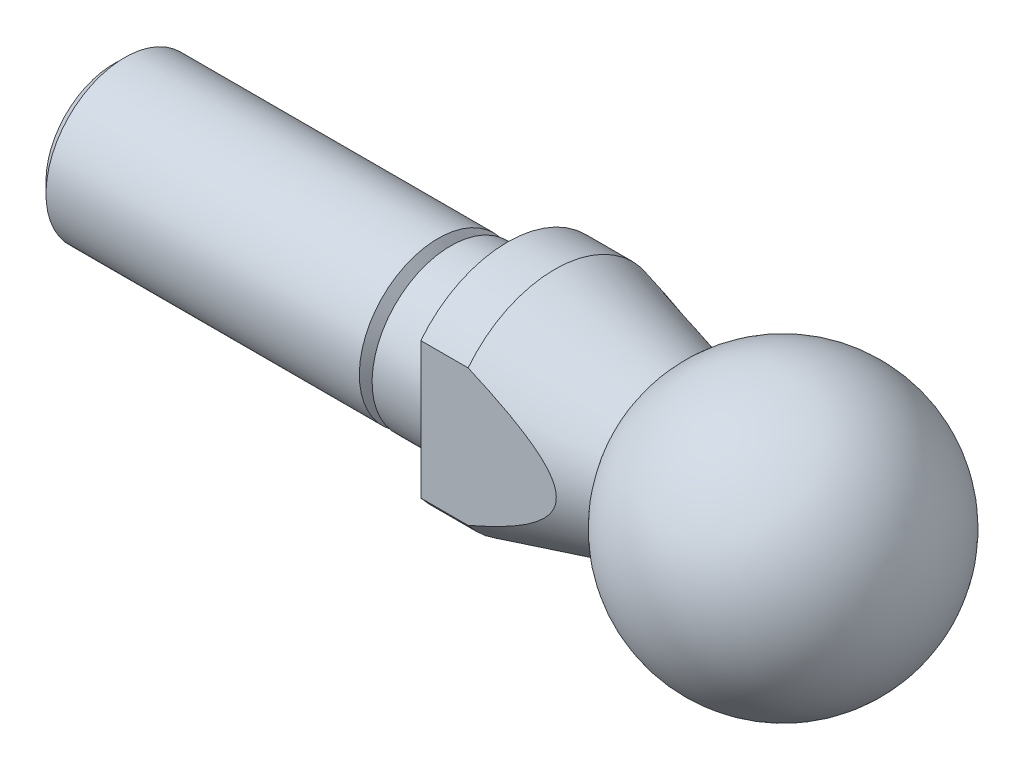
SolidWorks part; units mm, degrees
material "220M07"
ref_plane "Front Plane" through (0, 0, 0) normal (0, 0, 1) x (1, 0, 0)
ref_plane "Top Plane" through (0, 0, 0) normal (0, 1, 0) x (1, 0, 0)
ref_plane "Right Plane" through (0, 0, 0) normal (1, 0, 0) x (0, 0, -1)
sketch "Sketch1" plane through (0, 0, 0) normal (0, 0, 1) x (1, 0, 0)
  line L0 (-9.813, 0) -> (9.813, 0) construction
  line L3 (-14.5, 7) -> (-17.5, 7)
  line L4 (-17.5, 7) -> (-17.5, 5)
  line L5 (-17.5, 5) -> (-21.0959, 5)
  line L6 (-21.0959, 5) -> (-21.5, 4.3)
  line L7 (-21.5, 4.3) -> (-21.9041, 5)
  line L8 (-21.9041, 5) -> (-41.8, 5)
  line L10 (-42.5, 4.3) -> (-42.5, 0)
  line L11 (-42.5, 0) -> (8.75, 0)
  line L12 (-42.5, 4.3) -> (-41.8, 5)
  line L13 (-14.5, 7) -> (-7.1578, 5.0327)
  arc A0 (8.75, 0) -> (-7.1578, 5.0327) centre (0, 0) ccw
  point P4 (0, 0)
  dimension "D1" = 60
  dimension "Ball DIam" = 17.5
  dimension "Thd D" = 10
  dimension "Thd L" = 21
  dimension "D2" = 45
  dimension "Boss Diam" = 14
  dimension "Boss Thickness" = 3
  dimension "Centre L" = 42.5
  dimension "Thd Min" = 8.6
  dimension "D4" = 15
  dimension "Up To Shoulder" = 25
revolve "Body Revolve" add sketch "Sketch1" angle 360 about L0
ref_plane "Plane1" through (-7.1578, 0, 0) normal (1, 0, 0) x (0, 0, -1)
sketch "Sketch2" plane through (-17.5, 0, 0) normal (-1, 0, 0) x (0, 0, 1)
  line L1 (-5.5, -7) -> (5.5, -7)
  line L2 (-5.5, -7) -> (-5.5, 7)
  line L3 (-5.5, 7) -> (5.5, 7)
  line L4 (5.5, -7) -> (5.5, 7)
  line L5 (-5.5, -7) -> (5.5, 7) construction
  line L6 (-5.5, 7) -> (5.5, -7) construction
  circle A0 centre (0, 0) radius 7 construction
  point P0 (0, 0)
  dimension "S af" = 11
extrude "Cut-Extrude1" cut sketch "Sketch2" against normal up to surface (10.3422 mm away) flip side to cut up to plane "Plane1"
thread "Thread1" pitch 1 start angle 0, offset 2, length 0, pitch 1, diameter 6
ref_plane "Plane2" through (-28.95, 0, -3) normal (0, -1, 0) x (0, 0, -1)
sketch "Thread Profile1" plane through (-28.95, 0, -3) normal (0, -1, 0) x (0, 0, -1)
  line L0 (0, 0) -> (0, 1) construction
  line L11 (0, 0) -> (0, 0.875)
  line L12 (0, 0.875) -> (-0.5413, 0.5625)
  line L13 (-0.5413, 0.5625) -> (-0.5413, 0.3125)
  line L15 (-0.5413, 0.3125) -> (0, 0)
  line L17 (-0.5413, 0.4375) -> (0, 0.4375) construction
  point P2 (0, 0)
  dimension "Pitch" = 1
  dimension "Profile_Angle" = 60
  dimension "Profile_Land" = 0.25
  dimension "Profile_Height" = 0.5413
